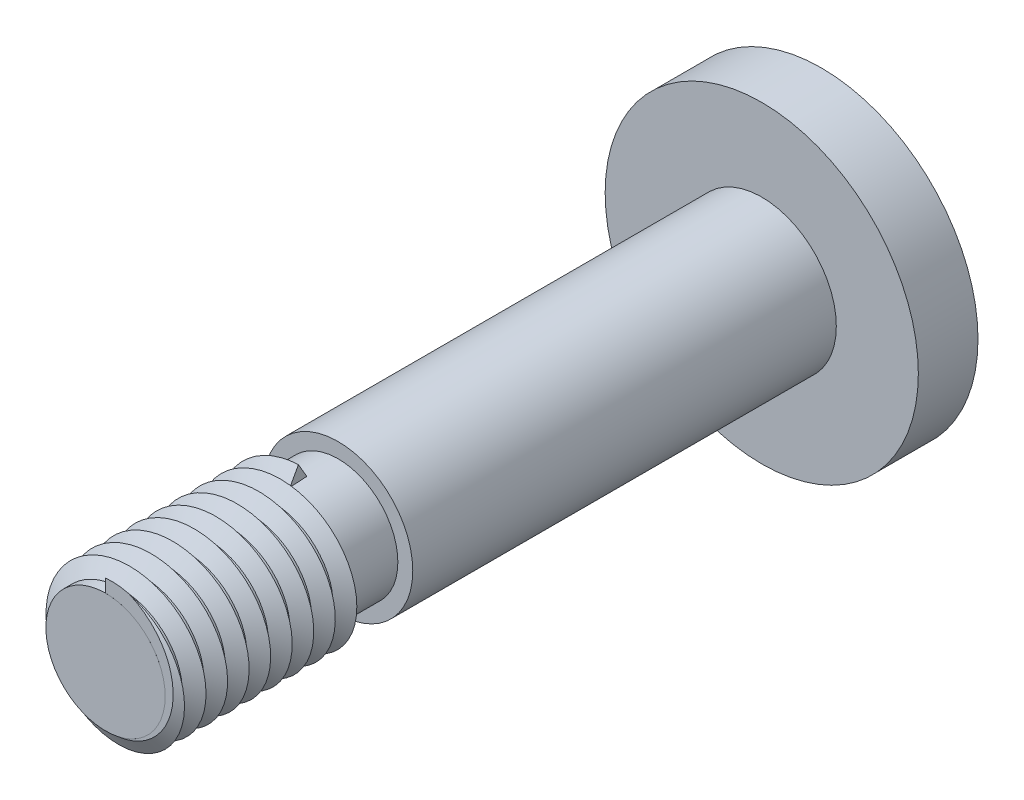
SolidWorks part; units mm, degrees
material "AISI 1035 Steel (SS)"
ref_plane "Front Plane" through (0, 0, 0) normal (0, 0, 1) x (1, 0, 0)
ref_plane "Top Plane" through (0, 0, 0) normal (0, 1, 0) x (1, 0, 0)
ref_plane "Right Plane" through (0, 0, 0) normal (1, 0, 0) x (0, 0, -1)
sketch "Sketch1" plane through (0, 0, 0) normal (0, 0, 1) x (1, 0, 0)
  circle A0 centre (0, 0) radius 3.175
  dimension "D1" = 6.35
extrude "Boss-Extrude1" add sketch "Sketch1" along normal blind 27.94
sketch "Sketch2" plane through (0, 0, 0) normal (0, 0, 1) x (1, 0, 0)
  circle A0 centre (0, 0) radius 6.6675
  dimension "D1" = 13.335
extrude "Boss-Extrude2" add sketch "Sketch2" against normal blind 2.54
sketch "Sketch3" plane through (0, 0, 27.94) normal (0, 0, 1) x (1, 0, 0)
  circle A0 centre (0, 0) radius 2.54
  circle A1 centre (0, 0) radius 3.175
  dimension "D1" = 5.08
extrude "Cut-Extrude1" cut sketch "Sketch3" against normal blind 9.906
sketch "Sketch4" plane through (0, 0, 27.94) normal (0, 0, 1) x (1, 0, 0)
  circle A0 centre (0, 0) radius 2.54
curve "Helix/Spiral1" pitch 0.9172 height 8.255 turns 9
ref_plane "Plane1" through (0, 2.54, 19.685) normal (0.9984, 0, -0.0574) x (-0.0574, 0, -0.9984)
sketch "Sketch5" plane through (0, 2.54, 19.685) normal (0.9984, 0, -0.0574) x (-0.0574, 0, -0.9984)
  line L0 (-0.4266, 0) -> (0.3354, 0)
  line L1 (1.6483, 0) -> (-8.2414, 0) construction
  line L2 (0.3354, 0) -> (-0.0456, 0.635)
  line L3 (-0.0456, 0.635) -> (-0.4266, 0)
  line L4 (-0.0456, 0) -> (-0.0456, 1.8291) construction
  dimension "D1" = 0.635
  dimension "D2" = 0.762
sweep "Sweep1" add profiles "Sketch5" path "Helix/Spiral1"
sketch "Sketch6" plane through (0, 0, 0) normal (0, 1, 0) x (1, 0, 0)
  line L0 (-2.54, -27.94) -> (2.54, -27.94) construction
  line L1 (1.2662, -27.94) -> (3.2921, -27.94)
  line L2 (1.2662, -27.94) -> (1.2662, -28.5214)
  line L3 (1.2662, -28.5214) -> (3.2921, -28.5214)
  line L4 (3.2921, -27.94) -> (3.2921, -28.5214)
  line L5 (0, 0) -> (0, -46.8262) construction
revolve "Cut-Revolve1" cut sketch "Sketch6" angle 360 about L5
